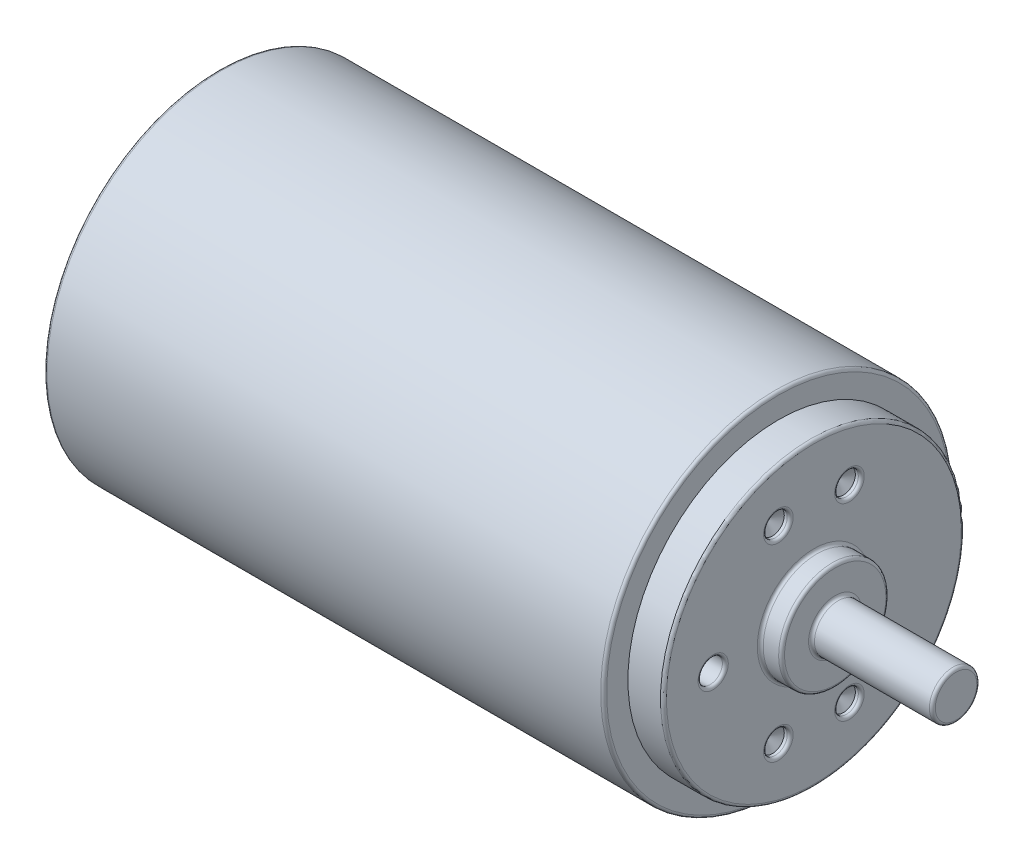
SolidWorks part; units mm, degrees
ref_plane "Ebene vorne" through (0, 0, 0) normal (0, 0, 1) x (1, 0, 0)
ref_plane "Ebene oben" through (0, 0, 0) normal (0, 1, 0) x (1, 0, 0)
ref_plane "Ebene rechts" through (0, 0, 0) normal (1, 0, 0) x (0, 0, -1)
sketch "Skizze1" plane through (0, 0, 0) normal (0, 0, 1) x (1, 0, 0)
  line L6 (-21.6511, 29.5) -> (72.8088, 29.5)
  line L7 (72.8088, 29.5) -> (72.8088, 25.3976)
  line L8 (72.8088, 25.3976) -> (78.8088, 25.3976)
  line L9 (78.8088, 25.3976) -> (78.8088, 9.0539)
  line L10 (87.8808, 4) -> (102.8088, 4)
  line L11 (102.8088, 4) -> (102.8088, 0)
  line L12 (102.8088, 0) -> (0, 0)
  line L13 (0, 0) -> (-39.1912, 0)
  line L14 (-21.6511, 29.5) -> (-21.6511, 22.9497)
  line L15 (-24.1912, 22.9497) -> (-21.6511, 22.9497)
  line L16 (-24.1912, 22.9497) -> (-24.1912, 5.6934)
  line L17 (-24.1912, 5.6934) -> (-30.1912, 4)
  line L18 (-30.1912, 4) -> (-39.1912, 4)
  line L19 (-39.1912, 4) -> (-39.1912, 0)
  line L20 (78.8088, 9.0539) -> (82.4088, 9.0539)
  line L21 (82.4088, 9.0539) -> (82.4088, 4)
  line L22 (82.4088, 4) -> (87.8808, 4)
  dimension "D1" = 103
  dimension "D2" = 142
  dimension "D3" = 4
  dimension "D4" = 6
  dimension "D5" = 3.6
  dimension "D6" = 20.4
  dimension "D7" = 29.5
  dimension "D8" = 4
  dimension "D9" = 15
revolve "Rotation1" add sketch "Skizze1" angle 360 about L13
hole_wizard "Ø4.0 (4) Durchmesser Bohrung1" positions "Skizze4" profile "Skizze3" hole size "Ø4.0" standard "ISO"
sketch "Skizze4" plane through (78.8088, 0, 0) normal (1, 0, 0) x (0, 0, -1)
  line L0 (0, 0) -> (0, 39.7142) construction
  line L1 (0, 39.7142) -> (0, 0) construction
  line L2 (0, 0) -> (0, -47.571) construction
  circle A0 centre (0, 0) radius 17 construction
  point P0 (-6, 15.906)
  point P2 (6, 15.906)
  point P6 (-6, -15.906)
  point P8 (6, -15.906)
  dimension "D1" = 34
  dimension "D2" = 6
  dimension "D3" = 6
  dimension "D4" = 6
  dimension "D5" = 6
sketch "Skizze3" plane through (78.8088, 15.906, 6) normal (0, 1, 0) x (0, 0, -1)
  line L0 (0, 0) -> (0, 2.2017)
  line L1 (0, 2.2017) -> (2, 1)
  line L2 (2, 1) -> (2, 0)
  line L5 (2, 0) -> (0, 0)
  line L10 (0, 2.2017) -> (-2, 1) construction
  line L11 (0, -6.35) -> (0, 107.95) construction
  dimension "Bohrerdurchmesser" = 4
  dimension "Bohrungstiefe" = 1
  dimension "Spitzenwinkel" = 118
hole_wizard "Ø4.1 (4.1) Durchmesser Bohrung1" positions "Skizze5" profile "Skizze6" hole size "Ø4.1" standard "ISO"
sketch "Skizze5" plane through (78.8088, 0, 0) normal (1, 0, 0) x (0, 0, -1)
  point P0 (-17, 0)
  dimension "D1" = 17
sketch "Skizze6" plane through (78.8088, 0, 17) normal (0, 1, 0) x (0, 0, -1)
  line L0 (0, 0) -> (0, 12.7318)
  line L1 (0, 12.7318) -> (2.05, 11.5)
  line L2 (2.05, 11.5) -> (2.05, 0)
  line L5 (2.05, 0) -> (0, 0)
  line L10 (0, 12.7318) -> (-2.05, 11.5) construction
  line L11 (0, -6.35) -> (0, 107.95) construction
  dimension "Bohrerdurchmesser" = 4.1
  dimension "Bohrungstiefe" = 11.5
  dimension "Spitzenwinkel" = 118
fillet "Verrundung1" radius 0.5 15 edges at (82.4088, 4, 0) (82.4088, 9.0539, 0) (78.8088, 9.0539, 0) (78.8088, 25.3976, 0) (78.8088, -15.906, -8) (78.8088, -15.906, 4) (78.8088, 15.906, -8) (78.8088, 15.906, 4) (78.8088, 0, 14.95) (102.8088, 4, 0) (72.8088, 29.5, 0) (-39.1912, 4, 0) (-24.1912, 22.9497, 0) (-21.6511, 22.9497, 0) (-21.6511, 29.5, 0)
